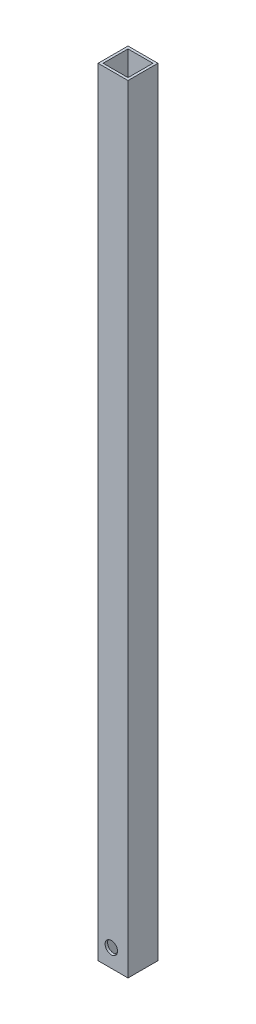
SolidWorks part; units mm, degrees
material "1060 Alloy"
ref_plane "Front Plane" through (0, 0, 0) normal (0, 0, 1) x (1, 0, 0)
ref_plane "Top Plane" through (0, 0, 0) normal (0, 1, 0) x (1, 0, 0)
ref_plane "Right Plane" through (0, 0, 0) normal (1, 0, 0) x (0, 0, -1)
sketch "Sketch1" plane through (0, 0, 0) normal (0, 1, 0) x (1, 0, 0)
  line L0 (-7.9375, 7.9375) -> (-7.9375, -7.9375)
  line L1 (-9.525, 9.525) -> (9.525, 9.525)
  line L2 (-9.525, 9.525) -> (-9.525, -9.525)
  line L3 (-9.525, -9.525) -> (9.525, -9.525)
  line L4 (9.525, 9.525) -> (9.525, -9.525)
  line L5 (-9.525, 9.525) -> (9.525, -9.525) construction
  line L6 (-9.525, -9.525) -> (9.525, 9.525) construction
  line L7 (-7.9375, -7.9375) -> (7.9375, -7.9375)
  line L8 (7.9375, 7.9375) -> (7.9375, -7.9375)
  line L9 (-7.9375, 7.9375) -> (7.9375, 7.9375)
  point P0 (0, 0)
  dimension "D1" = 19.05
  dimension "D2" = 19.05
  dimension "D3" = 1.5875
extrude "Boss-Extrude1" add sketch "Sketch1" along normal blind 495.3
sketch "Sketch2" plane through (0, 0, 9.525) normal (0, 0, 1) x (1, 0, 0)
  line L0 (-9.525, 0) -> (9.525, 0) construction
  line L1 (-9.525, 495.3) -> (-9.525, 0) construction
  circle A1 centre (-1.0954, 11.4523) radius 3.9688
  dimension "D3" = 7.9375
  dimension "D1" = 11.4523
  dimension "D2" = 8.4296
extrude "Cut-Extrude1" cut sketch "Sketch2" against normal up to surface (1.5875 mm away) up to face at (0, 247.65, 7.9375)
sketch "Sketch3" plane through (-9.525, 0, 0) normal (-1, 0, 0) x (0, 0, 1)
  line L0 (-9.525, 0) -> (9.525, 0) construction
  circle A0 centre (0, 9.525) radius 0.889
  dimension "D1" = 1.778
  dimension "D2" = 9.525
extrude "Cut-Extrude2" cut sketch "Sketch3" against normal up to next
